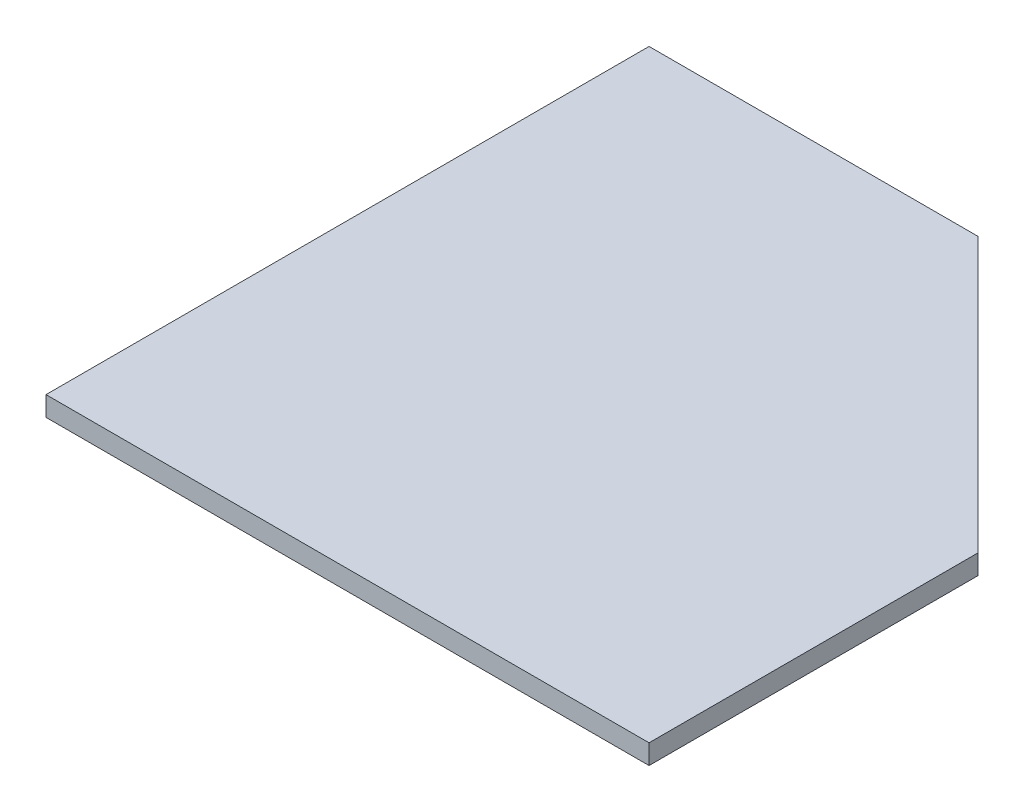
SolidWorks part; units mm, degrees
ref_plane "Спереди" through (0, 0, 0) normal (0, 0, 1) x (1, 0, 0)
ref_plane "Сверху" through (0, 0, 0) normal (0, 1, 0) x (1, 0, 0)
ref_plane "Справа" through (0, 0, 0) normal (1, 0, 0) x (0, 0, -1)
sketch "Эскиз1" plane through (0, 0, 0) normal (0, 1, 0) x (1, 0, 0)
  line L0 (0, 0) -> (0, 550)
  line L1 (0, 550) -> (300, 550)
  line L4 (550, 300) -> (550, 0)
  line L5 (550, 0) -> (0, 0)
  line L6 (300, 550) -> (550, 300)
extrude "Бобышка-Вытянуть1" add sketch "Эскиз1" along normal blind 18
